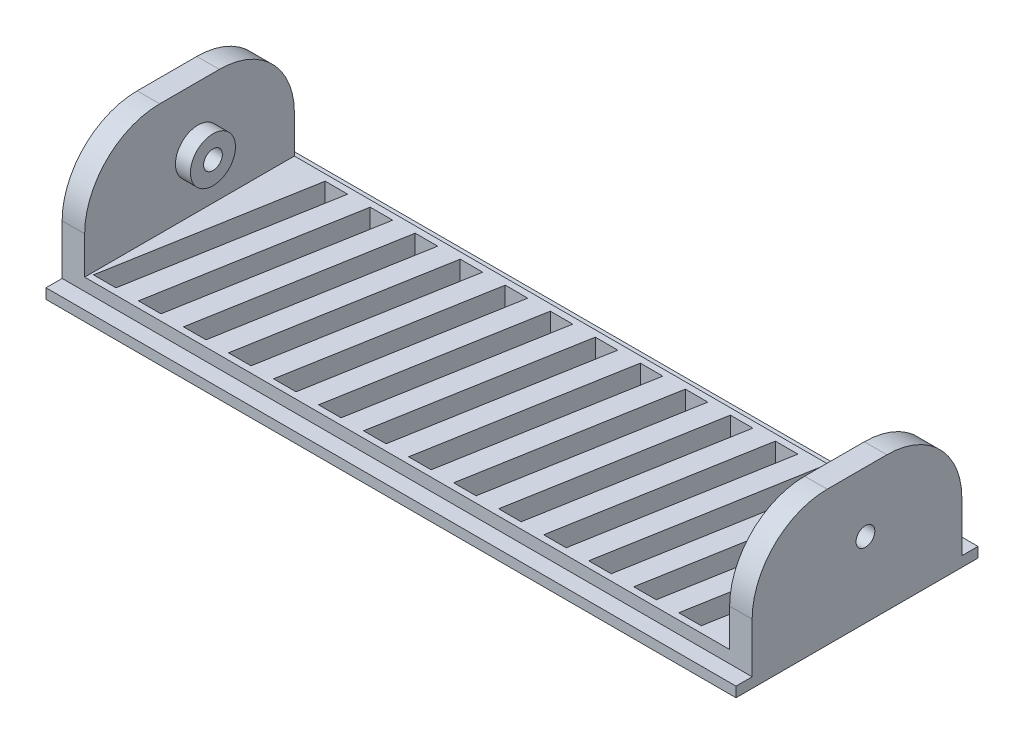
SolidWorks part; units mm, degrees
ref_plane "Front Plane" through (0, 0, 0) normal (0, 0, 1) x (1, 0, 0)
ref_plane "Top Plane" through (0, 0, 0) normal (0, 1, 0) x (1, 0, 0)
ref_plane "Right Plane" through (0, 0, 0) normal (1, 0, 0) x (0, 0, -1)
sketch "Sketch1" plane through (0, 0, 0) normal (0, 1, 0) x (1, 0, 0)
  line L1 (0, 0) -> (91.95, 0)
  line L2 (0, 0) -> (0, 32.25)
  line L3 (0, 32.25) -> (91.95, 32.25)
  line L4 (91.95, 0) -> (91.95, 32.25)
  dimension "D1" = 32.25
  dimension "D2" = 91.95
extrude "Boss-Extrude1" add sketch "Sketch1" along normal blind 3
sketch "Sketch2" plane through (0, 3, 0) normal (0, 1, 0) x (1, 0, 0)
  line L0 (0, -1.65) -> (0, 1.65) construction
  line L1 (91.95, 32.25) -> (0, 32.25)
  line L2 (91.95, 32.25) -> (91.95, 30.1)
  line L3 (91.95, 30.1) -> (0, 30.1)
  line L4 (0, 32.25) -> (0, 30.1)
  line L5 (-1.65, 0) -> (1.65, 0) construction
  line L6 (91.95, 0) -> (0, 0)
  line L7 (91.95, 0) -> (91.95, 2.15)
  line L8 (91.95, 2.15) -> (0, 2.15)
  line L9 (0, 0) -> (0, 2.15)
  line L10 (91.95, 0) -> (91.95, 32.25) construction
  dimension "D1" = 2.15
  dimension "D2" = 2.15
extrude "Cut-Extrude1" cut sketch "Sketch2" against normal blind 1.65
sketch "Sketch4" plane through (0, 3, 0) normal (0, 1, 0) x (1, 0, 0)
  line L0 (0, -9.9) -> (0, 9.9) construction
  line L1 (0, 30.1) -> (3, 30.1)
  line L2 (0, 30.1) -> (0, 2.15)
  line L3 (0, 2.15) -> (3, 2.15)
  line L4 (3, 30.1) -> (3, 2.15)
  line L5 (0, 30.1) -> (91.95, 30.1) construction
  line L6 (91.95, 2.15) -> (0, 2.15) construction
  line L7 (0, 30.1) -> (91.95, 30.1) construction
  line L8 (91.95, 30.1) -> (88.95, 30.1)
  line L9 (91.95, 30.1) -> (91.95, 2.15)
  line L10 (91.95, 2.15) -> (88.95, 2.15)
  line L11 (88.95, 30.1) -> (88.95, 2.15)
  line L12 (91.95, 2.15) -> (91.95, 30.1) construction
  line L13 (91.95, 2.15) -> (0, 2.15) construction
  dimension "D1" = 3
  dimension "D2" = 3
extrude "Boss-Extrude2" add sketch "Sketch4" along normal blind 15
sketch "Sketch5" plane through (0, 0, 0) normal (-1, 0, 0) x (0, 0, 1)
  line L0 (-32.25, 0) -> (0, 0) construction
  line L4 (-32.25, 1.35) -> (-32.25, 0) construction
  circle A0 centre (-17.25, 10) radius 1.25
  dimension "D2" = 2.5
  dimension "D1" = 10
  dimension "D3" = 15
extrude "Cut-Extrude2" cut sketch "Sketch5" against normal through all both and the other way through all
fillet "Fillet2" radius 10 4 edges at (90.45, 18, -2.15) (90.45, 18, -30.1) (1.5, 18, -2.15) (1.5, 18, -30.1)
sketch "Sketch7" plane through (0, 0, 0) normal (0, -1, 0) x (1, 0, 0)
  line L0 (88.95, -29.25) -> (85.95, -29.25)
  line L1 (88.95, -29.25) -> (84.3214, -3)
  line L2 (85.95, -29.25) -> (81.3214, -3)
  line L3 (84.3214, -3) -> (81.3214, -3)
  line L4 (82.95, -29.25) -> (79.95, -29.25)
  line L5 (82.95, -29.25) -> (78.3214, -3)
  line L6 (78.3214, -3) -> (75.3214, -3)
  line L7 (79.95, -29.25) -> (75.3214, -3)
  line L8 (3, -3) -> (3, -29.25)
  line L9 (3, -29.25) -> (88.95, -29.25)
  line L10 (88.95, -29.25) -> (88.95, -3)
  line L11 (88.95, -3) -> (3, -3)
  line L12 (3, -3) -> (3, -29.25)
  line L13 (3, -29.25) -> (88.95, -29.25)
  line L14 (88.95, -29.25) -> (88.95, -3)
  line L15 (88.95, -3) -> (3, -3)
  line L16 (76.95, -29.25) -> (73.95, -29.25)
  line L17 (76.95, -29.25) -> (72.3214, -3)
  line L18 (72.3214, -3) -> (69.3214, -3)
  line L19 (73.95, -29.25) -> (69.3214, -3)
  line L20 (70.95, -29.25) -> (67.95, -29.25)
  line L21 (70.95, -29.25) -> (66.3214, -3)
  line L22 (66.3214, -3) -> (63.3214, -3)
  line L23 (67.95, -29.25) -> (63.3214, -3)
  line L24 (64.95, -29.25) -> (61.95, -29.25)
  line L25 (64.95, -29.25) -> (60.3214, -3)
  line L26 (60.3214, -3) -> (57.3214, -3)
  line L27 (61.95, -29.25) -> (57.3214, -3)
  line L28 (58.95, -29.25) -> (55.95, -29.25)
  line L29 (58.95, -29.25) -> (54.3214, -3)
  line L30 (54.3214, -3) -> (51.3214, -3)
  line L31 (55.95, -29.25) -> (51.3214, -3)
  line L32 (52.95, -29.25) -> (49.95, -29.25)
  line L33 (52.95, -29.25) -> (48.3214, -3)
  line L34 (48.3214, -3) -> (45.3214, -3)
  line L35 (49.95, -29.25) -> (45.3214, -3)
  line L36 (46.95, -29.25) -> (43.95, -29.25)
  line L37 (46.95, -29.25) -> (42.3214, -3)
  line L38 (42.3214, -3) -> (39.3214, -3)
  line L39 (43.95, -29.25) -> (39.3214, -3)
  line L40 (40.95, -29.25) -> (37.95, -29.25)
  line L41 (40.95, -29.25) -> (36.3214, -3)
  line L42 (36.3214, -3) -> (33.3214, -3)
  line L43 (37.95, -29.25) -> (33.3214, -3)
  line L44 (34.95, -29.25) -> (31.95, -29.25)
  line L45 (34.95, -29.25) -> (30.3214, -3)
  line L46 (30.3214, -3) -> (27.3214, -3)
  line L47 (31.95, -29.25) -> (27.3214, -3)
  line L48 (28.95, -29.25) -> (25.95, -29.25)
  line L49 (28.95, -29.25) -> (24.3214, -3)
  line L50 (24.3214, -3) -> (21.3214, -3)
  line L51 (25.95, -29.25) -> (21.3214, -3)
  line L52 (22.95, -29.25) -> (19.95, -29.25)
  line L53 (22.95, -29.25) -> (18.3214, -3)
  line L54 (18.3214, -3) -> (15.3214, -3)
  line L55 (19.95, -29.25) -> (15.3214, -3)
  line L56 (16.95, -29.25) -> (13.95, -29.25)
  line L57 (16.95, -29.25) -> (12.3214, -3)
  line L58 (12.3214, -3) -> (9.3214, -3)
  line L59 (13.95, -29.25) -> (9.3214, -3)
  line L60 (10.95, -29.25) -> (7.95, -29.25)
  line L61 (10.95, -29.25) -> (6.3214, -3)
  line L62 (6.3214, -3) -> (3.3214, -3)
  line L63 (7.95, -29.25) -> (3.3214, -3)
  dimension "D1" = 3
  dimension "D2" = 3
  dimension "D3" = 80
  dimension "D4" = 14
extrude "Cut-Extrude5" cut sketch "Sketch7" against normal up to next contours L63 L13 L61 L15 | L55 L13 L53 L15 | L51 L13 L49 L15 | L47 L13 L45 L15 | L43 L13 L41 L15 | L39 L13 L37 L15 | L31 L13 L29 L15 | L23 L13 L21 L15 | L7 L4 L5 L6 | L1 L3 L2 L0 | L57 L58 L59 L56 | L35 L34 L33 L32 | L27 L26 L25 L24 | L19 L18 L17 L16
sketch "Sketch8" plane through (3, 0, 0) normal (1, 0, 0) x (0, 0, -1)
  circle A0 centre (17.25, 10) radius 3
  dimension "D1" = 6
extrude "Boss-Extrude3" add sketch "Sketch8" along normal blind 2
ref_plane "Plane1" through (45.975, 0, 0) normal (1, 0, 0) x (0, 0, -1)
mirror "Mirror1" about plane through (45.975, 0, 0) normal (1, 0, 0) of "Boss-Extrude3"
sketch "Sketch9" plane through (0, 0, 0) normal (-1, 0, 0) x (0, 0, 1)
  circle A0 centre (-17.25, 10) radius 1.25
  dimension "D1" = 2.5
extrude "Cut-Extrude6" cut sketch "Sketch9" against normal through all both and the other way through all
equation "\"side panel width\"= 32.25"
equation "\"D1@Sketch1\"=\"side panel width\""
equation "\"side panel length\"= 91.95"
equation "\"D2@Sketch1\"=\"side panel length\""
equation "\"length of bevels\"=2.15"
equation "\"D1@Sketch2\"=\"length of bevels\""
equation "\"D2@Sketch2\"=\"length of bevels\""
equation "\"thickness of wall\"=3"
equation "\"D1@Sketch4\"=\"thickness of wall\""
equation "\"D2@Sketch4\"=\"thickness of wall\""
equation "\"m3 tap size\"=2.5"
equation "\"D2@Sketch5\"=\"m3 tap size\""
equation "\"D3@Sketch7\"=80"
equation "\"D1@Sketch5\"=10"
equation "\"D3@Sketch5\"=15"
equation "\"D1@Sketch8\"=6"
equation "\"D1@Sketch9\"=\"m3 tap size\""
